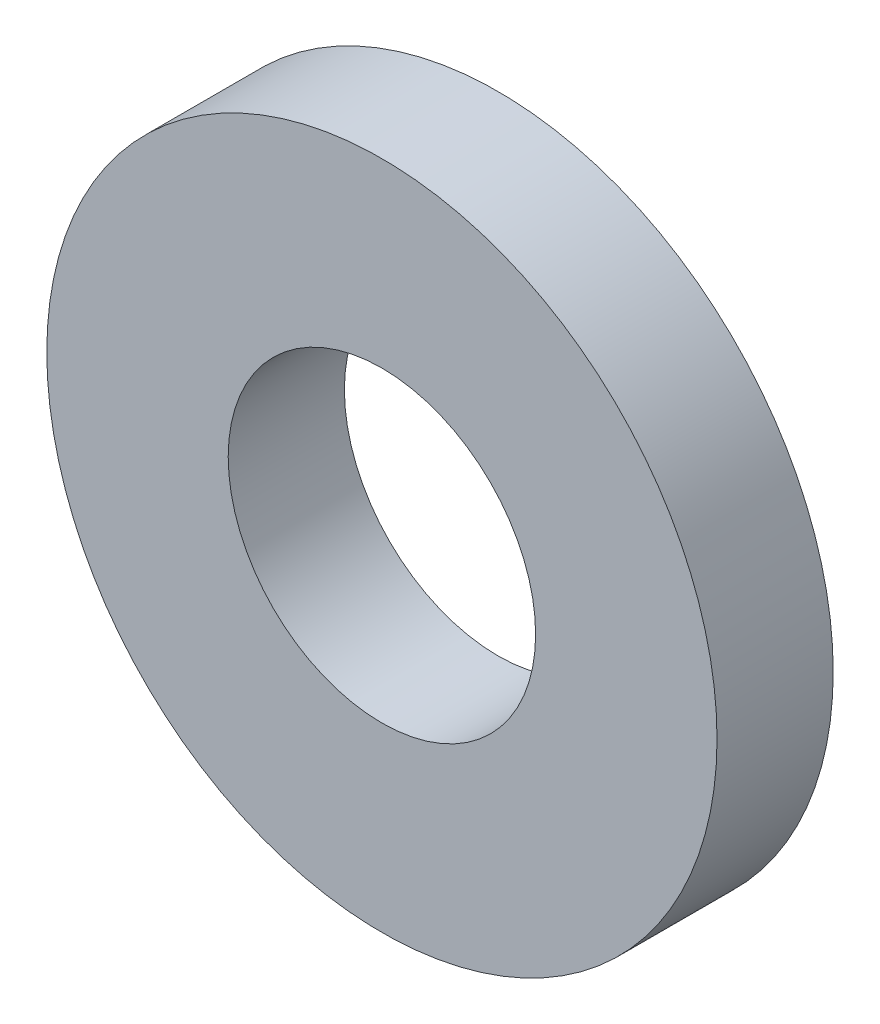
SolidWorks part; units mm, degrees
ref_plane "Front Plane" through (0, 0, 0) normal (0, 0, 1) x (1, 0, 0)
ref_plane "Top Plane" through (0, 0, 0) normal (0, 1, 0) x (1, 0, 0)
ref_plane "Right Plane" through (0, 0, 0) normal (1, 0, 0) x (0, 0, -1)
sketch "Sketch1" plane through (0, 0, 0) normal (0, 0, 1) x (1, 0, 0)
  circle A0 centre (0, 0) radius 4.7625
  circle A1 centre (0, 0) radius 2.1844
  dimension "D1" = 9.525
  dimension "D2" = 4.3688
extrude "Extrude1" add sketch "Sketch1" along normal blind 1.651
